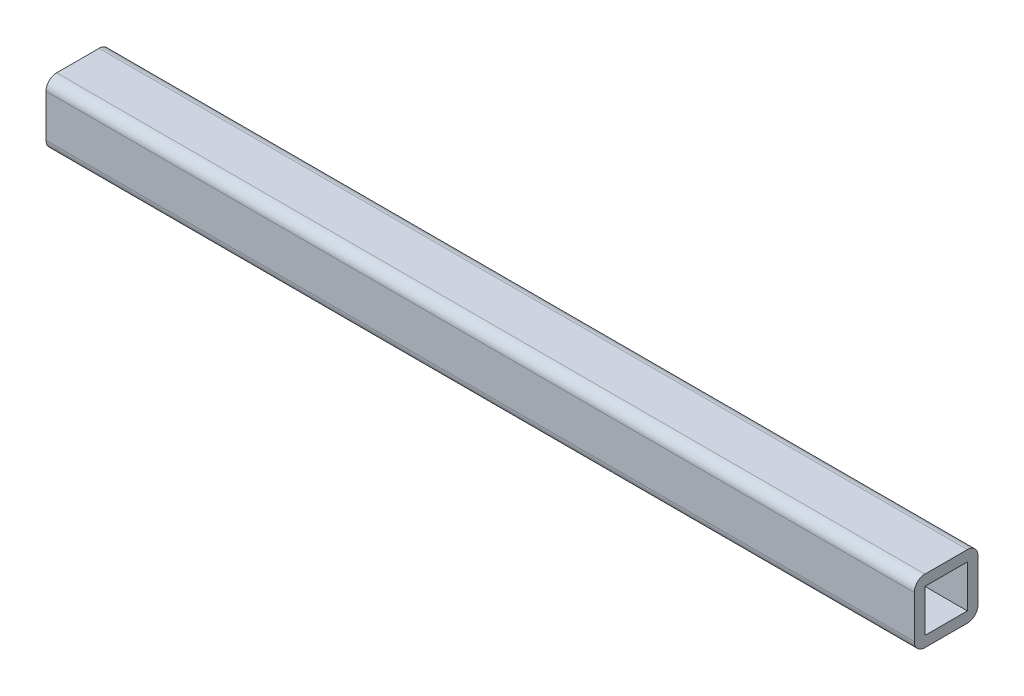
SolidWorks part; units mm, degrees
material "Plain Carbon Steel"
ref_plane "Front" through (0, 0, 0) normal (0, 0, 1) x (1, 0, 0)
ref_plane "Top" through (0, 0, 0) normal (0, 1, 0) x (1, 0, 0)
ref_plane "Right" through (0, 0, 0) normal (1, 0, 0) x (0, 0, -1)
sketch "Sketch1" plane through (0, 0, 0) normal (1, 0, 0) x (0, 0, -1)
  line L1 (-19.05, -19.05) -> (19.05, -19.05)
  line L2 (-19.05, -19.05) -> (-19.05, 19.05)
  line L3 (-19.05, 19.05) -> (19.05, 19.05)
  line L4 (19.05, -19.05) -> (19.05, 19.05)
  line L5 (-19.05, -19.05) -> (19.05, 19.05) construction
  line L6 (-19.05, 19.05) -> (19.05, -19.05) construction
  line L7 (-12.7, -12.7) -> (12.7, -12.7)
  line L8 (-12.7, -12.7) -> (-12.7, 12.7)
  line L9 (-12.7, 12.7) -> (12.7, 12.7)
  line L10 (12.7, -12.7) -> (12.7, 12.7)
  line L11 (-12.7, -12.7) -> (12.7, 12.7) construction
  line L12 (-12.7, 12.7) -> (12.7, -12.7) construction
  point P0 (0, 0)
  point P6 (0, 0)
  dimension "D1" = 38.1
  dimension "D2" = 38.1
  dimension "D3" = 6.35
extrude "Boss-Extrude1" add sketch "Sketch1" along normal mid plane 519.1125
fillet "Fillet1" radius 6.35 4 edges at (0, -19.05, -19.05) (0, -19.05, 19.05) (0, 19.05, -19.05) (0, 19.05, 19.05)
equation "\"Total Cutting Length\"= \"Cutting Length-Outer\" + \"Cutting Length-Inner\""
equation "\"Amount in ft^2\"= \"Bounding Box Area-Blank\" / 144"
